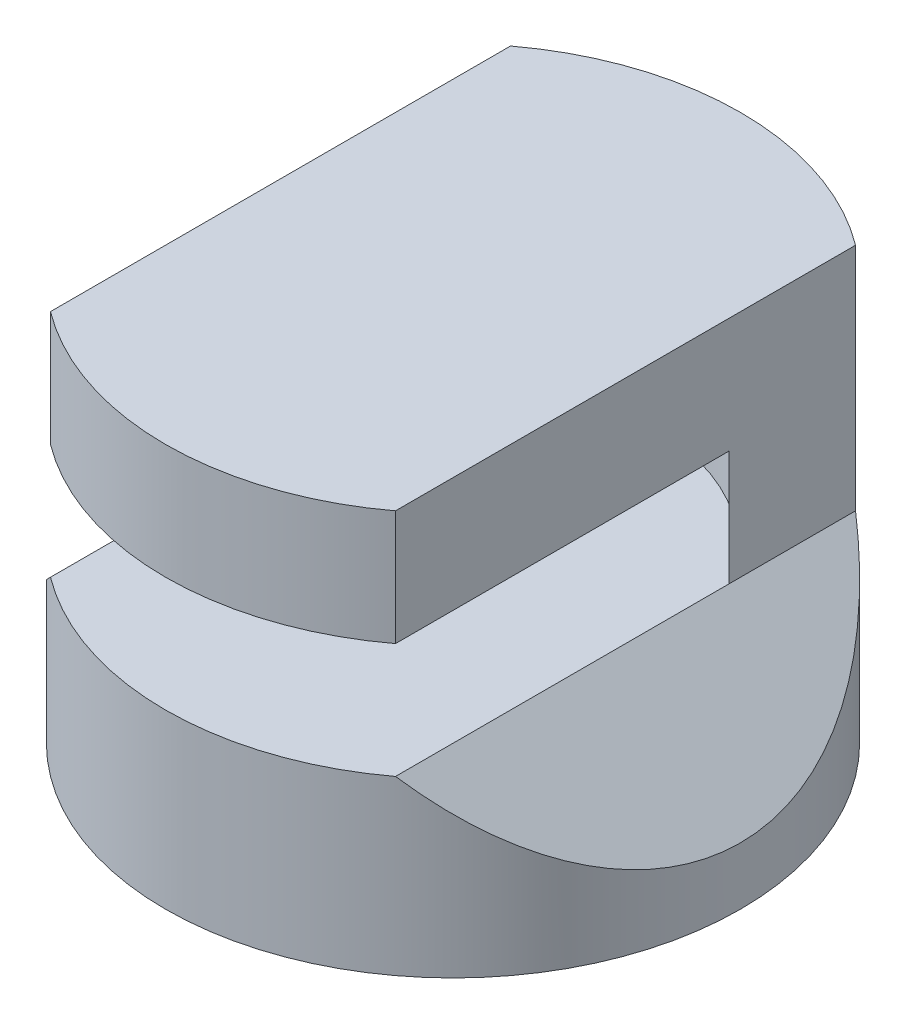
SolidWorks part; units mm, degrees
ref_plane "Front Plane" through (0, 0, 0) normal (0, 0, 1) x (1, 0, 0)
ref_plane "Top Plane" through (0, 0, 0) normal (0, 1, 0) x (1, 0, 0)
ref_plane "Right Plane" through (0, 0, 0) normal (1, 0, 0) x (0, 0, -1)
sketch "Sketch1" plane through (0, 0, 0) normal (0, 0, 1) x (1, 0, 0)
  line L1 (0, 0) -> (100, 0)
  line L2 (0, 0) -> (0, 80)
  line L3 (0, 80) -> (100, 80)
  line L4 (100, 0) -> (100, 80)
  dimension "D1" = 100
  dimension "D2" = 80
extrude "Boss-Extrude2" add sketch "Sketch1" along normal blind 100
sketch "Sketch2" plane through (0, 0, 0) normal (0, 0, 1) x (1, 0, 0)
  line L0 (0, 80) -> (20, 80)
  line L1 (0, 0) -> (20, 0)
  line L2 (0, 0) -> (0, 10)
  line L3 (0, 10) -> (20, 10)
  line L4 (20, 0) -> (20, 10)
  line L5 (100, 0) -> (80, 0)
  line L6 (100, 0) -> (100, 10)
  line L7 (100, 10) -> (80, 10)
  line L8 (80, 0) -> (80, 10)
  line L9 (20, 80) -> (20, 40)
  line L10 (20, 40) -> (0, 20)
  line L11 (0, 80) -> (0, 0) construction
  line L12 (0, 20) -> (0, 80)
  line L13 (80, 80) -> (100, 80)
  line L14 (100, 80) -> (0, 80) construction
  line L15 (100, 80) -> (100, 20)
  line L16 (100, 0) -> (100, 80) construction
  line L17 (80, 80) -> (80, 40)
  line L18 (80, 40) -> (100, 20)
  dimension "D1" = 20
  dimension "D2" = 10
  dimension "D3" = 20
  dimension "D4" = 10
  dimension "D5" = 20
  dimension "D6" = 10
  dimension "D7" = 40
  dimension "D8" = 40
  dimension "D9" = 20
  dimension "D10" = 10
extrude "Cut-Extrude1" cut sketch "Sketch2" along normal blind 100
ref_plane "Plane1" through (0, 80, 0) normal (0, 1, 0) x (1, 0, 0)
sketch "Sketch3" plane through (0, 80, 0) normal (0, 1, 0) x (1, 0, 0)
  line L0 (80, -100) -> (20, -100) construction
  line L1 (0, -50) -> (0, -100)
  line L2 (0, -100) -> (100, -100)
  line L3 (100, -100) -> (100, 0)
  line L4 (100, 0) -> (0, 0)
  line L5 (0, 0) -> (0, -50)
  circle A0 centre (50, -50) radius 50
  dimension "D1" = 100
  dimension "D2" = 50
  dimension "D3" = 50
  dimension "D4" = 100
  dimension "D5" = 50
  dimension "D6" = 50
extrude "Cut-Extrude2" cut sketch "Sketch3" against normal blind 100 contours A0 L4 L5 | A0 L3 L4 | A0 L2 L3 | A0 L1 L2
sketch "Sketch4" plane through (0, 0, 0) normal (1, 0, 0) x (0, 0, -1)
  line L1 (0, 0) -> (-15, 0)
  line L2 (0, 0) -> (0, 10)
  line L3 (0, 10) -> (-15, 10)
  line L4 (-15, 0) -> (-15, 10)
  line L5 (-100, 0) -> (-85, 0)
  line L6 (-100, 0) -> (-100, 10)
  line L7 (-100, 10) -> (-85, 10)
  line L8 (-85, 0) -> (-85, 10)
  dimension "D1" = 15
  dimension "D2" = 10
  dimension "D3" = 15
  dimension "D4" = 0
  dimension "D5" = 10
  dimension "D6" = 0
extrude "Cut-Extrude5" cut sketch "Sketch4" along normal blind 100
ref_plane "Plane3" through (0, 60, 0) normal (0, 1, 0) x (1, 0, 0)
sketch "Sketch7" plane through (0, 60, 0) normal (0, 1, 0) x (1, 0, 0)
  line L0 (50, -85) -> (15, -85)
  line L1 (15, -85) -> (15, -15)
  line L2 (15, -15) -> (85, -15)
  line L3 (85, -15) -> (85, -85)
  line L4 (85, -85) -> (50, -85)
  circle A0 centre (50, -50) radius 35
  dimension "D1" = 70
extrude "Cut-Extrude16" cut sketch "Sketch7" against normal blind 20 contours A0 L1 L0 | A0 L3 L2 | A0 L4 L3 | A0 L2 L1 | A0
sketch "Sketch8" plane through (0, 80, 0) normal (0, 1, 0) x (1, 0, 0)
  line L0 (50, -15) -> (20, -15)
  line L1 (20, -15) -> (20, -85)
  line L2 (20, -90) -> (20, -10) construction
  line L3 (20, -85) -> (80, -85)
  line L4 (80, -85) -> (80, -15)
  line L5 (80, -90) -> (80, -10) construction
  line L6 (80, -15) -> (50, -15)
  circle A0 centre (50, -50) radius 35
  arc A1 (20, -90) -> (80, -90) centre (50, -50) ccw construction
  arc A3 (80, -10) -> (20, -10) centre (50, -50) ccw construction
  point P2 (50, -100)
  line M1 (20, -10) -> (20, -90)
  line M3 (80, -90) -> (80, -10)
  dimension "D1" = 70
  dimension "D2" = 50
  dimension "D3" = 0
  dimension "D4" = 30
  dimension "D5" = 60
extrude "Boss-Extrude3" add sketch "Sketch8" against normal blind 40 contours A0 L0 M1 | A0 L6 M3 | A0 L3 M1 | A0 L3 M3
sketch "Sketch9" plane through (0, 0, 0) normal (0, -1, 0) x (1, 0, 0)
  line L0 (20, 68.0278) -> (20, 85)
  line L1 (20, 85) -> (80, 85)
  line L2 (80, 85) -> (80, 15)
  line L3 (80, 15) -> (20, 15)
  line L4 (20, 15) -> (20, 68.0278)
  circle A0 centre (50, 50) radius 35
  line M1 (80, 85) -> (20, 85)
  line M2 (20, 85) -> (20, 15)
  line M3 (20, 15) -> (80, 15)
  line M4 (80, 15) -> (80, 85)
  dimension "D1" = 70
extrude "Cut-Extrude17" cut sketch "Sketch9" against normal blind 10 contours A0 L1 M2 | A0 M4 M1 | A0 L3 M4 | A0 L4 M3
ref_plane "Plane10" through (0, 0, 50) normal (0, 0, 1) x (1, 0, 0)
sketch "Sketch18" plane through (0, 0, 50) normal (0, 0, 1) x (1, 0, 0)
  line L0 (20, 40) -> (20, 60) construction
  line L1 (20, 60) -> (80, 60)
  line L2 (20, 60) -> (20, 40)
  line L3 (20, 40) -> (80, 40)
  line L4 (80, 60) -> (80, 40)
  dimension "D1" = 60
  dimension "D2" = 20
  dimension "D3" = 0
  dimension "D4" = 0
extrude "Cut-Extrude22" cut sketch "Sketch18" along normal blind 75
equation "\"cm\"=40"
